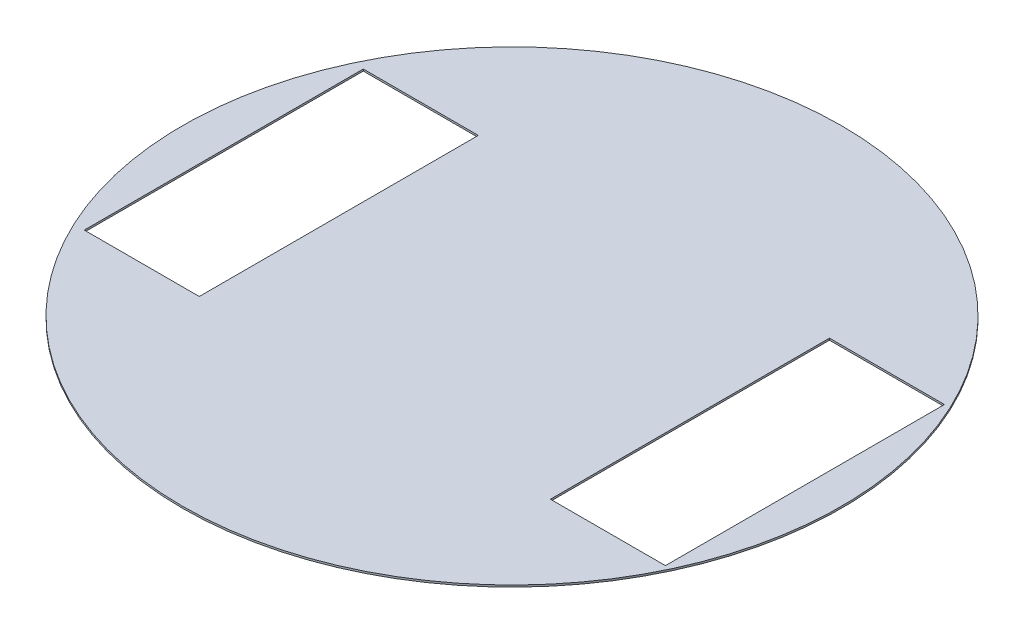
SolidWorks part; units mm, degrees
ref_plane "Front Plane" through (0, 0, 0) normal (0, 0, 1) x (1, 0, 0)
ref_plane "Top Plane" through (0, 0, 0) normal (0, 1, 0) x (1, 0, 0)
ref_plane "Right Plane" through (0, 0, 0) normal (1, 0, 0) x (0, 0, -1)
sketch "Sketch1" plane through (0, 0, 0) normal (0, 1, 0) x (1, 0, 0)
  line L0 (-80, 38.1) -> (0, 38.1)
  line L1 (0, 38.1) -> (0, 0)
  line L10 (-80, 38.1) -> (-48.5914, 38.1)
  line L11 (-80, 38.1) -> (-80, -38.1)
  line L12 (-80, -38.1) -> (-48.5914, -38.1)
  line L13 (-48.5914, 38.1) -> (-48.5914, -38.1)
  line L14 (-80, 38.1) -> (-48.5914, -38.1) construction
  line L15 (-80, -38.1) -> (-48.5914, 38.1) construction
  line L16 (48.5914, 38.1) -> (80, 38.1)
  line L17 (48.5914, 38.1) -> (48.5914, -38.1)
  line L18 (48.5914, -38.1) -> (80, -38.1)
  line L19 (80, 38.1) -> (80, -38.1)
  line L20 (48.5914, 38.1) -> (80, -38.1) construction
  line L21 (48.5914, -38.1) -> (80, 38.1) construction
  circle A0 centre (0, 0) radius 90
extrude "Boss-Extrude1" add sketch "Sketch1" along normal blind 0.5 contours A0
sketch "Sketch3" plane through (0, 0.5, 0) normal (0, 1, 0) x (1, 0, 0)
  line L3 (80, 38.1) -> (80, -38.1)
  line L4 (80, -38.1) -> (48.5914, -38.1)
  line L6 (48.5914, -38.1) -> (80, -38.1)
  line L7 (48.5914, -38.1) -> (48.5914, 38.1)
  line L8 (48.5914, 38.1) -> (80, 38.1)
  line L9 (80, -38.1) -> (80, 38.1)
  line L11 (-78.7097, 38.1) -> (-47.301, 38.1)
  line L12 (-78.7097, 38.1) -> (-78.7097, -38.1)
  line L13 (-78.7097, -38.1) -> (-47.301, -38.1)
  line L14 (-47.301, 38.1) -> (-47.301, -38.1)
extrude "Cut-Extrude2" cut sketch "Sketch3" against normal blind 1 contours L8 L7 L4 L3 | L14 L11 L12 L13
